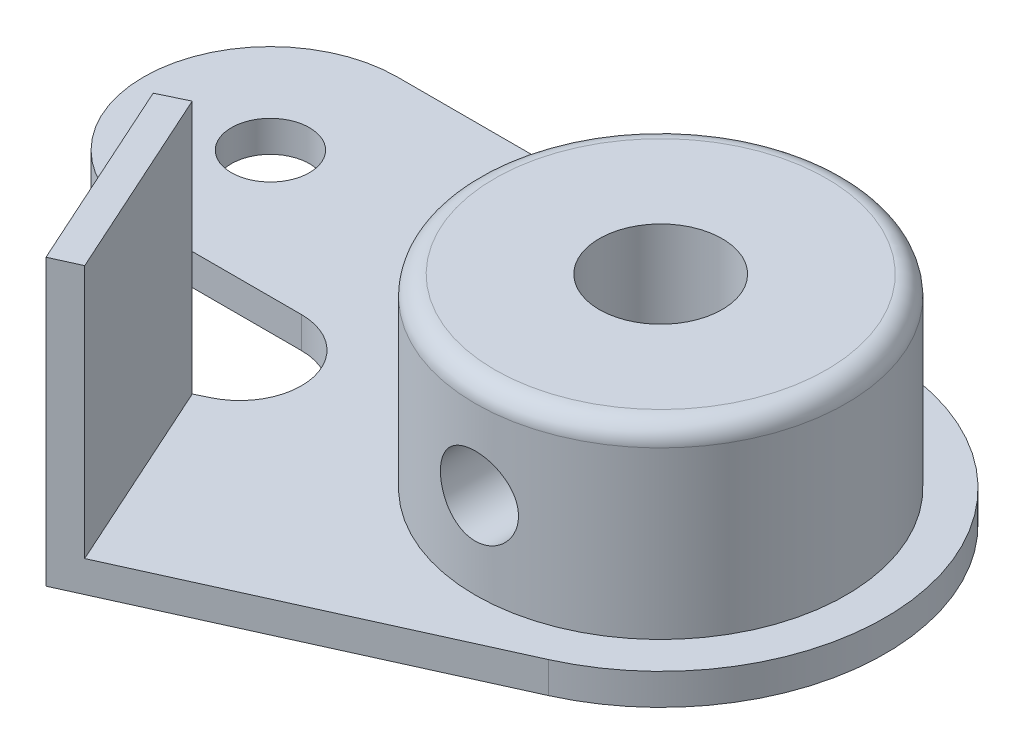
SolidWorks part; units mm, degrees
material "AISI 1020"
ref_plane "Plan de face" through (0, 0, 0) normal (0, 0, 1) x (1, 0, 0)
ref_plane "Plan de dessus" through (0, 0, 0) normal (0, 1, 0) x (1, 0, 0)
ref_plane "Plan de droite" through (0, 0, 0) normal (1, 0, 0) x (0, 0, -1)
sketch "Esquisse1" plane through (0, 0, 0) normal (0, 1, 0) x (1, 0, 0)
  line L0 (0, 11.5) -> (-25, 11.5)
  line L1 (-15.5325, -7.5102) -> (-17.5325, -8.4772)
  line L2 (-25, -1.5) -> (-16.9092, -1.5)
  line L3 (4.7385, -10.4784) -> (-13, -18.5)
  line L4 (-17.5325, -8.4772) -> (-13, -18.5)
  arc A0 (4.7385, -10.4784) -> (0, 11.5) centre (0, 0) ccw
  arc A1 (-25, 11.5) -> (-25, -1.5) centre (-25, 5) ccw
  arc A2 (-16.9092, -1.5) -> (-15.5325, -7.5102) centre (-16.9092, -4.6628) cw
  circle A3 centre (0, 0) radius 3.15
  circle A4 centre (-25, 5) radius 2
  point P10 (11.5, 0)
  point P11 (-31.5, 5)
  dimension "D1" = 23
  dimension "D2" = 6.5
  dimension "D8" = 6.3
  dimension "D9" = 4
  dimension "D3" = 43
  dimension "D4" = 13
  dimension "D5" = 30
  dimension "D6" = 2
extrude "Boss.-Extru.1" add sketch "Esquisse1" along normal blind 1.6
sketch "Esquisse2" plane through (0, 1.6, 0) normal (0, 1, 0) x (1, 0, 0)
  circle A0 centre (0, 0) radius 9.5
  circle A1 centre (0, 0) radius 3.15
  dimension "D1" = 19
extrude "Boss.-Extru.2" add sketch "Esquisse2" along normal blind 9.5
fillet "Congé1" radius 1 1 edges at (0, 11.1, 9.5)
sketch "Esquisse3" plane through (0, 1.6, 0) normal (0, 1, 0) x (1, 0, 0)
  line L0 (-17.5325, -8.4772) -> (-13, -18.5)
  line L1 (-13, -18.5) -> (-11.6337, -17.8821)
  line L2 (-16.182, -7.8242) -> (-11.6337, -17.8821)
  line L3 (-13, -18.5) -> (4.7385, -10.4784) construction
  line L4 (-15.5325, -7.5102) -> (-17.5325, -8.4772) construction
  line L5 (-16.182, -7.8242) -> (-17.5325, -8.4772)
  dimension "D1" = 1.5
extrude "Boss.-Extru.3" add sketch "Esquisse3" along normal blind 13
sketch "Esquisse4" plane through (0, 0, 0) normal (0, 0, 1) x (1, 0, 0)
  circle A0 centre (0, 6) radius 2
  dimension "D1" = 4
  dimension "D2" = 6
extrude "Enlèv. mat.-Extru.1" cut sketch "Esquisse4" along normal through all
